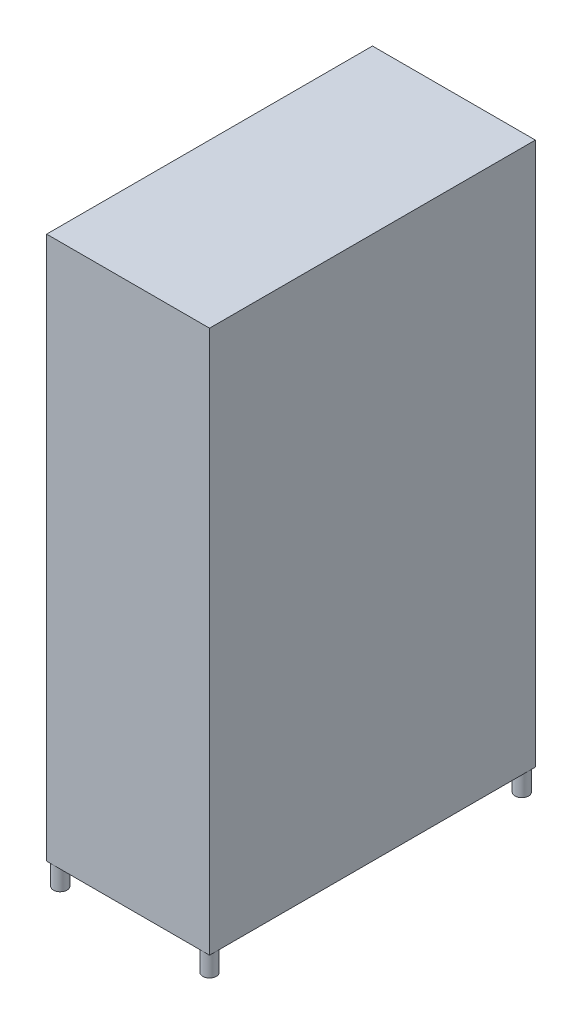
SolidWorks part; units mm, degrees
material "红木"
ref_plane "前视基准面" through (0, 0, 0) normal (0, 0, 1) x (1, 0, 0)
ref_plane "上视基准面" through (0, 0, 0) normal (0, 1, 0) x (1, 0, 0)
ref_plane "右视基准面" through (0, 0, 0) normal (1, 0, 0) x (0, 0, -1)
sketch "草图1" plane through (0, 0, 0) normal (0, 1, 0) x (1, 0, 0)
  line L1 (-300, -600) -> (300, -600)
  line L2 (-300, -600) -> (-300, 600)
  line L3 (-300, 600) -> (300, 600)
  line L4 (300, -600) -> (300, 600)
  line L5 (-300, -600) -> (300, 600) construction
  line L6 (-300, 600) -> (300, -600) construction
  point P0 (0, 0)
  dimension "D1" = 600
  dimension "D2" = 1200
extrude "凸台-拉伸1" add sketch "草图1" along normal blind 2000
sketch "草图2" plane through (0, 0, 0) normal (0, -1, 0) x (1, 0, 0)
  line L0 (300, 600) -> (300, -600) construction
  line L2 (-300, 600) -> (300, 600) construction
  circle A0 centre (275, 575) radius 25
  dimension "D1" = 50
extrude "凸台-拉伸2" add sketch "草图2" along normal blind 80
mirror "镜向1" about plane through (0, 0, 0) normal (1, 0, 0) of "凸台-拉伸2"
mirror "镜向2" about plane through (0, 0, 0) normal (0, 0, 1) of "镜向1", "凸台-拉伸2"
